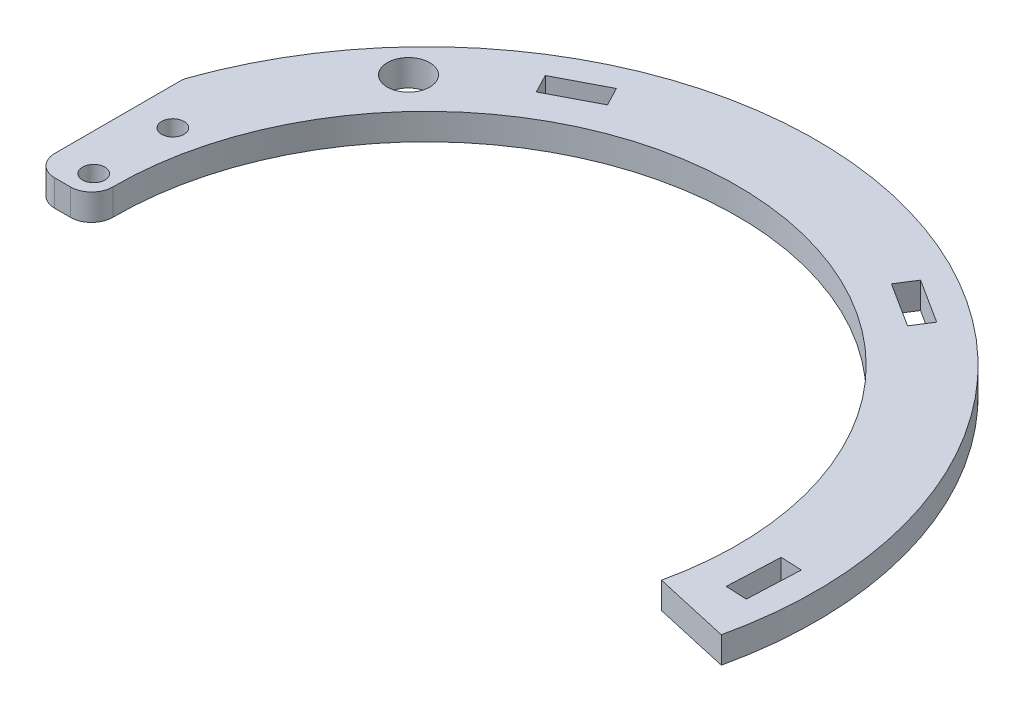
SolidWorks part; units mm, degrees
ref_plane "Front Plane" through (0, 0, 0) normal (0, 0, 1) x (1, 0, 0)
ref_plane "Top Plane" through (0, 0, 0) normal (0, 1, 0) x (1, 0, 0)
ref_plane "Right Plane" through (0, 0, 0) normal (1, 0, 0) x (0, 0, -1)
sketch "Sketch1" plane through (0, 0, 0) normal (0, 1, 0) x (1, 0, 0)
  line L0 (0, 0) -> (-63, 0) construction
  line L1 (-47.7573, 56.5264) -> (-38.0768, 45.0684)
  line L2 (0, 0) -> (-49.3664, 46.0349) construction
  line L15 (-63, -30) -> (-63, 30) construction
  line L16 (-55.5, 0) -> (-70.5, 0) construction
  line L17 (-70.4495, -22.6467) -> (-56.1692, -18.0562)
  circle A0 centre (0, 0) radius 55 construction
  circle A1 centre (0, 0) radius 62.5 construction
  circle A2 centre (-49.3664, 46.0349) radius 3.75 construction
  circle A5 centre (-49.3664, 46.0349) radius 4.025
  circle A7 centre (-63, 0) radius 2.125
  circle A8 centre (-63, -15) radius 2.125
  circle A9 centre (-63, 15) radius 2.125
  arc A10 (-38.0768, 45.0684) -> (-56.1692, -18.0562) centre (0, 0) ccw
  arc A11 (-47.7573, 56.5264) -> (-70.4495, -22.6467) centre (0, 0) ccw
  point P7 (-63, 0)
  dimension "D1" = 110
  dimension "D4" = 125
  dimension "D5" = 7.5
  dimension "D11" = 15
  dimension "D12" = 15
  dimension "D13" = 8.05
  dimension "D8" = 4.25
  dimension "D10" = 5
  dimension "D2" = 59
  dimension "D9" = 15
  dimension "D14" = 8
  dimension "D3" = 63
  dimension "D6" = 67.5
  dimension "D7" = 43
extrude "Boss-Extrude1" add sketch "Sketch1" along normal blind 5
sketch "Sketch2" plane through (0, 5, 0) normal (0, 1, 0) x (1, 0, 0)
  line L0 (0, 0) -> (-84.4523, 0) construction
  line L2 (-70, 27.6661) -> (-98.9046, 27.6661)
  line L3 (-70, 27.6661) -> (-70, -27.6661)
  line L4 (-70, -27.6661) -> (-98.9046, -27.6661)
  line L5 (-98.9046, 27.6661) -> (-98.9046, -27.6661)
  line L6 (-84.4523, -27.6661) -> (-84.4523, 27.6661) construction
  line L7 (-70, 0) -> (-98.9046, 0) construction
  dimension "D1" = 70
extrude "Cut-Extrude1" cut sketch "Sketch2" against normal through all both and the other way through all
sketch "Sketch3" plane through (0, 5, 0) normal (0, 1, 0) x (1, 0, 0)
  line L0 (-70, -22.5022) -> (-70, 24) construction
  line L1 (-70, -4.3988) -> (-45.7929, -4.3988)
  line L2 (-70, -4.3988) -> (-70, -25.4993)
  line L3 (-70, -25.4993) -> (-45.7929, -25.4993)
  line L4 (-45.7929, -4.3988) -> (-45.7929, -25.4993)
  line L5 (-57.8964, -25.4993) -> (-57.8964, -4.3988) construction
  line L6 (-70, -14.949) -> (-45.7929, -14.949) construction
  point P56 (-57.8964, -14.949)
extrude "Cut-Extrude2" cut sketch "Sketch3" against normal through all both and the other way through all
fillet "Fillet1" radius 4 5 edges at (-70, 2.5, -24) (-70, 2.5, 4.3988) (-58.8358, 2.5, 4.3988) (-38.0768, 2.5, -45.0684) (-47.7573, 2.5, -56.5264)
sketch "Sketch4" plane through (0, 0, 0) normal (0, 1, 0) x (1, 0, 0)
  line L0 (0, 0) -> (0, 52) construction
  line L1 (0, 0) -> (-24.0109, 46.1246)
  line L2 (0, 0) -> (51.9505, -2.2682)
  line L3 (0, 0) -> (27.9396, 43.8564)
  line L4 (57.5639, -12.9382) -> (72.1988, -16.2275)
  line L5 (-54.3492, 50.2211) -> (-43.5327, 51.526)
  line L6 (-40.5762, 48.0267) -> (-45.1021, 53.3836) construction
  line L7 (-43.5327, 51.526) -> (-46.3672, 36.484)
  circle A0 centre (0, 0) radius 45 construction
  circle A1 centre (0, 0) radius 52 construction
  arc A2 (-46.3672, 36.484) -> (57.5639, -12.9382) centre (0, 0) cw
  arc A3 (-40.8615, 42.5599) -> (-58.9988, -0.3735) centre (0, 0) ccw construction
  arc A4 (-54.3492, 50.2211) -> (72.1988, -16.2275) centre (0, 0) cw
  arc A5 (-50.9094, 53.7051) -> (-69.7714, 24.6566) centre (0, 0) ccw construction
  dimension "D1" = 90
  dimension "D2" = 104
  dimension "D3" = 60
  dimension "D4" = 60
  dimension "D5" = 32.5
extrude "Boss-Extrude2" add sketch "Sketch4" along normal up to surface (5 mm away) contours A4 L5 L7 A2 L4 up to face at (-58.0257, 5, -23.8616)
sketch "Sketch5" plane through (0, 5, 0) normal (0, 1, 0) x (1, 0, 0)
  line L0 (0, 0) -> (-34.1694, 65.6388) construction
  line L1 (0, 0) -> (39.7602, 62.411) construction
  line L2 (0, 0) -> (73.9296, -3.2278) construction
  line L3 (0, 0) -> (-24.0109, 46.1246) construction
  line L4 (0, 0) -> (27.9396, 43.8564) construction
  line L5 (0, 0) -> (51.9505, -2.2682) construction
  line L6 (-36.2957, 58.895) -> (-34.4487, 55.347)
  line L7 (-36.2957, 58.895) -> (-27.4256, 63.5125)
  line L8 (-34.4487, 55.347) -> (-25.5786, 59.9644)
  line L9 (-27.4256, 63.5125) -> (-25.5786, 59.9644)
  line L10 (-36.2957, 58.895) -> (-25.5786, 59.9644) construction
  line L11 (-34.4487, 55.347) -> (-27.4256, 63.5125) construction
  arc A0 (72.1988, -16.2275) -> (-54.3492, 50.2211) centre (0, 0) ccw construction
  arc A1 (57.5639, -12.9382) -> (-46.3672, 36.484) centre (0, 0) ccw construction
  point P15 (-30.9372, 59.4297)
  point P22 (0, 0)
  dimension "D1" = 4
  dimension "D2" = 65
  dimension "D3" = 10
extrude "Cut-Extrude3" cut sketch "Sketch5" against normal through all
pattern_circular "CirPattern1" count 3 every 60 about axis through (0, 0, 0) along (0, 1, 0) of "Cut-Extrude3"
